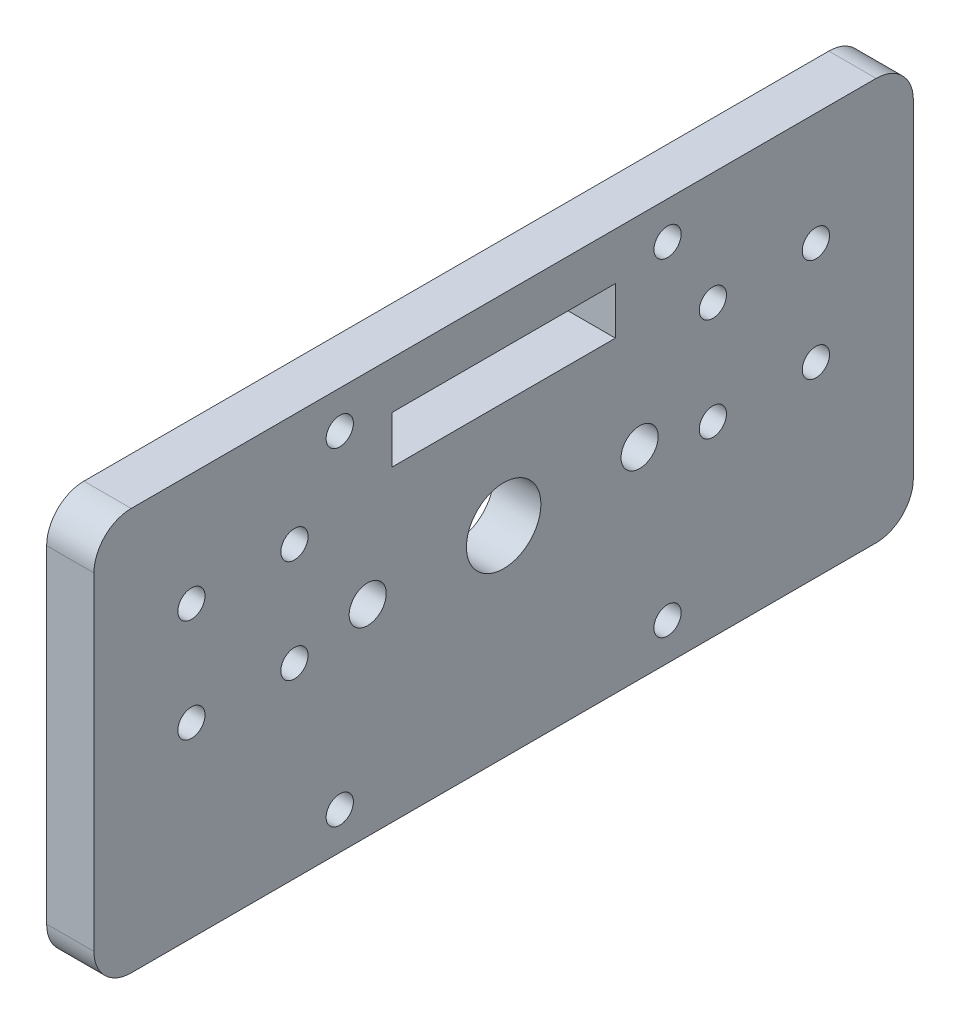
SolidWorks part; units mm, degrees
ref_plane "Front Plane" through (0, 0, 0) normal (0, 0, 1) x (1, 0, 0)
ref_plane "Top Plane" through (0, 0, 0) normal (0, 1, 0) x (1, 0, 0)
ref_plane "Right Plane" through (0, 0, 0) normal (1, 0, 0) x (0, 0, -1)
sketch "Sketch1" plane through (0, 0, 0) normal (1, 0, 0) x (0, 0, -1)
  line L1 (-55, -27) -> (55, -27)
  line L2 (-55, -27) -> (-55, 27)
  line L3 (-55, 27) -> (55, 27)
  line L4 (55, -27) -> (55, 27)
  line L5 (-55, -27) -> (55, 27) construction
  line L6 (-55, 27) -> (55, -27) construction
  point P0 (0, 0)
  dimension "D1" = 54
  dimension "D2" = 110
extrude "Boss-Extrude1" add sketch "Sketch1" along normal blind 6.35
fillet "Fillet1" radius 5 4 edges at (3.175, 27, -55) (3.175, 27, 55) (3.175, -27, -55) (3.175, -27, 55)
sketch "Sketch2" plane through (6.35, 0, 0) normal (1, 0, 0) x (0, 0, -1)
  line L1 (-22, -22) -> (22, -22) construction
  line L2 (-22, -22) -> (-22, 22) construction
  line L3 (-22, 22) -> (22, 22) construction
  line L4 (22, -22) -> (22, 22) construction
  line L5 (-22, -22) -> (22, 22) construction
  line L6 (-22, 22) -> (22, -22) construction
  point P0 (0, 0)
  dimension "D1" = 44
  dimension "D2" = 44
hole_wizard "#6 Clearance Hole1" positions "Sketch4" profile "Sketch3" hole size "#6" standard "ANSI Inch" end condition through all
sketch "Sketch4" plane through (6.35, 0, 0) normal (1, 0, 0) x (0, 0, -1)
  point P0 (-22, 22)
  point P3 (22, 22)
  point P6 (22, -22)
  point P9 (-22, -22)
sketch "Sketch3" plane through (6.35, 22, 22) normal (0, 1, 0) x (0, 0, -1)
  line L0 (0, 0) -> (0, 6.35)
  line L1 (0, 6.35) -> (1.8288, 6.35)
  line L2 (1.8288, 6.35) -> (1.8288, 0)
  line L5 (1.8288, 0) -> (0, 0)
  line L11 (0, -6.35) -> (0, 107.95) construction
  dimension "Thru Hole Dia." = 3.6576
  dimension "Thru Hole Depth" = 6.35
sketch "Sketch5" plane through (6.35, 0, 0) normal (1, 0, 0) x (0, 0, -1)
  circle A0 centre (0, 0) radius 5
  dimension "D1" = 10
extrude "Cut-Extrude1" cut sketch "Sketch5" against normal through all
sketch "Sketch7" plane through (6.35, 0, 0) normal (1, 0, 0) x (0, 0, -1)
  line L0 (-41.9148, -1.9448) -> (-41.9148, 11.8848) construction
  line L1 (-41.9148, -1.9448) -> (-28.0852, -1.9448) construction
  line L2 (-41.9148, 11.8848) -> (-28.0852, 11.8848) construction
  line L3 (-28.0852, -1.9448) -> (-28.0852, 11.8848) construction
  line L4 (-41.9148, -1.9448) -> (-28.0852, 11.8848) construction
  line L5 (-41.9148, 11.8848) -> (-28.0852, -1.9448) construction
  line L6 (41.9148, -1.9448) -> (41.9148, 11.8848) construction
  line L7 (41.9148, -1.9448) -> (28.0852, -1.9448) construction
  line L8 (41.9148, 11.8848) -> (28.0852, 11.8848) construction
  line L9 (28.0852, -1.9448) -> (28.0852, 11.8848) construction
  line L10 (41.9148, -1.9448) -> (28.0852, 11.8848) construction
  line L11 (41.9148, 11.8848) -> (28.0852, -1.9448) construction
  line L12 (-35, 4.97) -> (35, 4.97) construction
  line L13 (50, 27) -> (-50, 27) construction
  point P1 (-35, 4.97)
  point P2 (35, 4.97)
  point P8 (0, 4.97)
  dimension "D1" = 19.558
  dimension "D2" = 19.558
  dimension "D3" = 70
  dimension "D4" = 22.03
hole_wizard "#6 Clearance Hole2" positions "Sketch9" profile "Sketch8" hole size "#6" standard "ANSI Inch" end condition through all
sketch "Sketch9" plane through (6.35, 0, 0) normal (1, 0, 0) x (0, 0, -1)
  point P0 (-41.9148, 11.8848)
  point P3 (-28.0852, 11.8848)
  point P6 (-28.0852, -1.9448)
  point P9 (-41.9148, -1.9448)
  point P12 (28.0852, 11.8848)
  point P15 (28.0852, -1.9448)
  point P18 (41.9148, -1.9448)
  point P21 (41.9148, 11.8848)
sketch "Sketch8" plane through (6.35, 11.8848, 41.9148) normal (0, 1, 0) x (0, 0, -1)
  line L0 (0, 0) -> (0, 6.35)
  line L1 (0, 6.35) -> (1.8288, 6.35)
  line L2 (1.8288, 6.35) -> (1.8288, 0)
  line L5 (1.8288, 0) -> (0, 0)
  line L11 (0, -6.35) -> (0, 107.95) construction
  dimension "Thru Hole Dia." = 3.6576
  dimension "Thru Hole Depth" = 6.35
sketch "Sketch10" plane through (0, 0, 0) normal (-1, 0, 0) x (0, 0, 1)
  line L0 (15, 14.3) -> (15, 20.65)
  line L1 (15, 14.3) -> (-15, 14.3)
  line L2 (15, 20.65) -> (-15, 20.65)
  line L3 (-15, 14.3) -> (-15, 20.65)
  line L4 (15, 14.3) -> (-15, 20.65) construction
  line L5 (15, 20.65) -> (-15, 14.3) construction
  line L7 (-50, 27) -> (50, 27) construction
  point P1 (0, 17.475)
  dimension "D1" = 30
  dimension "D2" = 6.35
  dimension "D3" = 6.35
extrude "Cut-Extrude2" cut sketch "Sketch10" against normal through all
sketch "Sketch11" plane through (0, 0, 0) normal (-1, 0, 0) x (0, 0, 1)
  line L0 (-18.25, 0) -> (18.25, 0) construction
  point P4 (0, 0)
  dimension "D1" = 36.5
hole_wizard "#10 Clearance Hole1" positions "Sketch13" profile "Sketch12" hole size "#10" standard "ANSI Inch" end condition through all
sketch "Sketch13" plane through (0, 0, 0) normal (-1, 0, 0) x (0, 0, 1)
  point P0 (18.25, 0)
  point P3 (-18.25, 0)
sketch "Sketch12" plane through (0, 0, 18.25) normal (0, 1, 0) x (0, 0, 1)
  line L0 (0, 0) -> (0, 6.35)
  line L1 (0, 6.35) -> (2.4892, 6.35)
  line L2 (2.4892, 6.35) -> (2.4892, 0)
  line L5 (2.4892, 0) -> (0, 0)
  line L11 (0, -6.35) -> (0, 107.95) construction
  dimension "Thru Hole Dia." = 4.9784
  dimension "Thru Hole Depth" = 6.35
